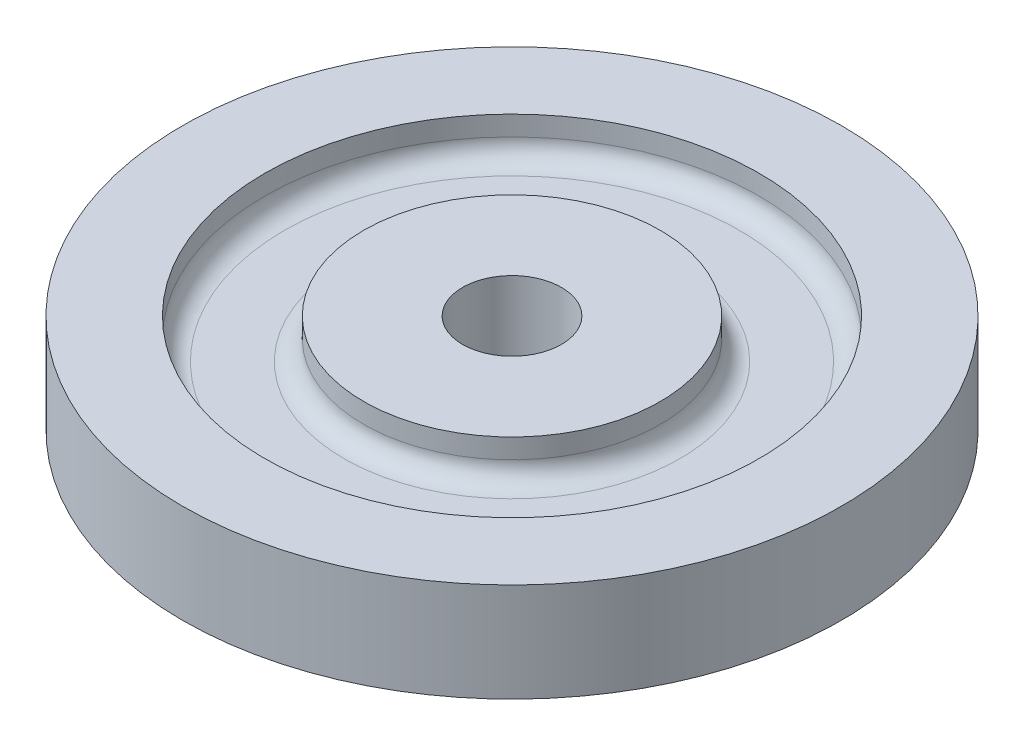
SolidWorks part; units mm, degrees
ref_plane "Front Plane" through (0, 0, 0) normal (0, 0, 1) x (1, 0, 0)
ref_plane "Top Plane" through (0, 0, 0) normal (0, 1, 0) x (1, 0, 0)
ref_plane "Right Plane" through (0, 0, 0) normal (1, 0, 0) x (0, 0, -1)
sketch "Sketch1" plane through (0, 0, 0) normal (0, 1, 0) x (1, 0, 0)
  circle A0 centre (0, 0) radius 6.35
  circle A1 centre (0, 0) radius 12.7
  circle A2 centre (0, 0) radius 25.4
  circle A3 centre (0, 0) radius 42.3291
  dimension "D1" = 12.7
  dimension "D2" = 25.4
  dimension "D3" = 50.8
  dimension "D4" = 84.6582
extrude "Boss-Extrude1" add sketch "Sketch1" along normal blind 12.7 contours A3 A2 | A2 A1 | A0 | A1 A0
sketch "Sketch3" plane through (0, 12.7, 0) normal (0, 1, 0) x (1, 0, 0)
  circle A0 centre (0, 0) radius 25.4
  dimension "D1" = 50.8
sketch "Sketch4" plane through (0, 0, 0) normal (0, 0, 1) x (1, 0, 0)
  line L1 (-31.75, 12.7) -> (-19.05, 12.7)
  line L2 (-31.75, 12.7) -> (-31.75, 10.16)
  line L3 (-29.21, 7.62) -> (-21.59, 7.62)
  line L4 (-19.05, 12.7) -> (-19.05, 10.16)
  arc A0 (-21.59, 7.62) -> (-19.05, 10.16) centre (-21.59, 10.16) ccw
  arc A1 (-31.75, 10.16) -> (-29.21, 7.62) centre (-29.21, 10.16) ccw
  point P4 (-25.4, 12.7)
  point P5 (0, 0)
  point P11 (-19.05, 7.62)
  dimension "D3" = 2.54
  dimension "D1" = 5.08
  dimension "D2" = 12.7
sweep "Cut-Sweep5" cut profiles "Sketch4" path "Sketch3"
